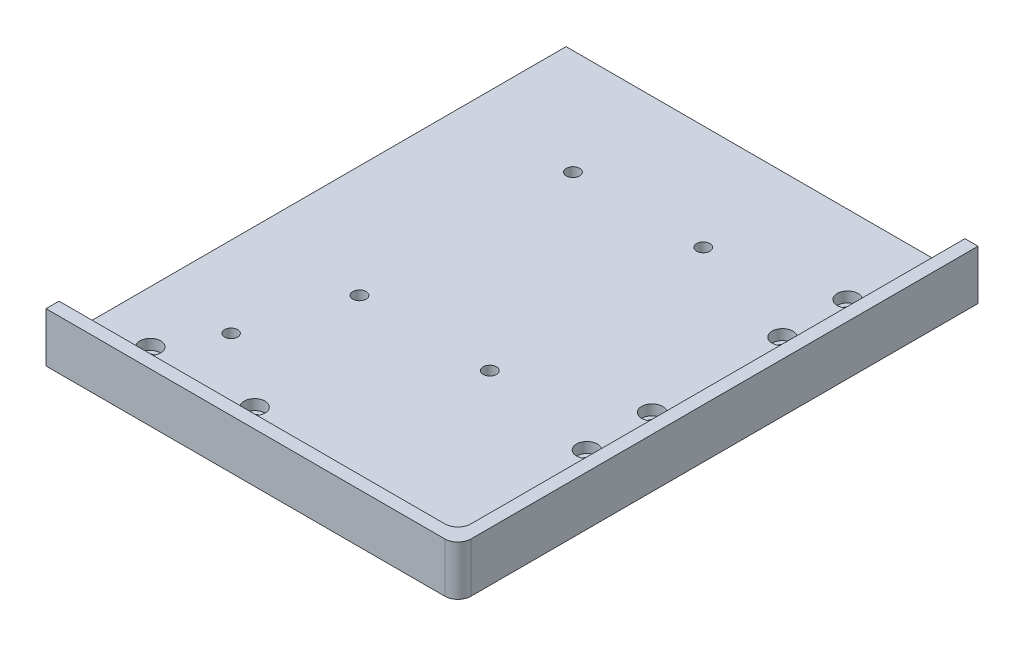
SolidWorks part; units mm, degrees
ref_plane "Front Plane" through (0, 0, 0) normal (0, 0, 1) x (1, 0, 0)
ref_plane "Top Plane" through (0, 0, 0) normal (0, 1, 0) x (1, 0, 0)
ref_plane "Right Plane" through (0, 0, 0) normal (1, 0, 0) x (0, 0, -1)
sketch "Sketch1" plane through (0, 0, 0) normal (0, 1, 0) x (1, 0, 0)
  line L1 (0, 0) -> (158, 0)
  line L2 (0, 0) -> (0, -199.5)
  line L3 (0, -199.5) -> (158, -199.5)
  line L4 (158, 0) -> (158, -199.5)
  dimension "D1" = 158
  dimension "D2" = 199.5
extrude "Boss-Extrude1" add sketch "Sketch1" along normal blind 6.35
sketch "Sketch2" [suppressed] plane through (0, 6.35, 0) normal (0, 1, 0) x (1, 0, 0)
  line L0 (0, -199.5) -> (158, -199.5) construction
  line L1 (158, -199.5) -> (77, -199.5)
  line L2 (158, -199.5) -> (158, -158.5)
  line L3 (158, -158.5) -> (77, -158.5)
  line L4 (77, -199.5) -> (77, -158.5)
  dimension "D1" = 81
  dimension "D2" = 41
sketch "Sketch3" plane through (0, 6.35, 0) normal (0, 1, 0) x (1, 0, 0)
  line L16 (158, -199.5) -> (158, 0) construction
  line L20 (0, -199.5) -> (158, -199.5) construction
  line L21 (158, -199.5) -> (158, 0)
  line L22 (0, -199.5) -> (158, -199.5)
  line L23 (0, -194.5) -> (153, -194.5)
  line L24 (153, -194.5) -> (153, 0)
  line L25 (158, 0) -> (153, 0)
  line L26 (0, -199.5) -> (0, -194.5)
  dimension "D1" = 5
extrude "Boss-Extrude2" add sketch "Sketch3" along normal blind 12.7
sketch "Sketch4" plane through (0, 6.35, 0) normal (0, -1, 0) x (1, 0, 0)
  line L0 (0, 179.5) -> (80, 179.5) construction
  line L1 (0, 0) -> (0, 199.5) construction
  line L3 (0, 199.5) -> (158, 199.5) construction
  line L4 (40, 179.5) -> (40, 188.5903) construction
  line L5 (138, 160) -> (138, 0) construction
  line L7 (158, 0) -> (0, 0) construction
  line L8 (158, 199.5) -> (158, 0) construction
  line L9 (138, 80) -> (152.6176, 80) construction
  point P8 (20, 179.5)
  point P11 (60, 179.5)
  point P20 (138, 130)
  point P21 (138, 105)
  point P22 (138, 30)
  point P23 (138, 80)
  point P24 (138, 55)
  dimension "D1" = 20
  dimension "D2" = 40
  dimension "D3" = 20
  dimension "D4" = 25
  dimension "D5" = 25
  dimension "D6" = 80
  dimension "D7" = 160
hole_wizard "CBORE for M4 SHCS1" positions "Sketch4" profile "Sketch5" counterbore size "M4" standard "ANSI Metric" end condition up to next
sketch "Sketch5" plane through (138, 6.35, 55) normal (1, 0, 0) x (0, 0, 1)
  line L0 (0, 0) -> (0, 6.35)
  line L1 (0, 6.35) -> (2.25, 6.35)
  line L3 (2.25, 6.35) -> (2.25, 4)
  line L4 (2.25, 4) -> (4, 4)
  line L5 (4, 4) -> (4, 0)
  line L7 (4, 0) -> (0, 0)
  line L11 (0, -6.35) -> (0, 107.95) construction
  dimension "Thru Hole Dia." = 4.5
  dimension "Thru Hole Depth" = 6.35
  dimension "C'Bore Dia." = 8
  dimension "C'Bore Depth" = 4
sketch "Sketch7" [suppressed] plane through (0, 0, 0) normal (0, 0, -1) x (-1, 0, 0)
  line L0 (-79, 19.05) -> (-79, 4.7647) construction
  line L1 (-158, 19.05) -> (0, 19.05) construction
  line L2 (-158, 19.05) -> (-158, 0) construction
  line L3 (-129, 19.05) -> (0, 19.05)
  line L4 (-129, 19.05) -> (-129, 9.05)
  line L5 (-129, 9.05) -> (0, 9.05)
  line L6 (0, 19.05) -> (0, 9.05)
  line L7 (0, 19.05) -> (0, 0) construction
  dimension "D2" = 10
  dimension "D3" = 29
extrude "Cut-Extrude2" [suppressed] cut sketch "Sketch7" against normal up to next
fillet "Fillet1" [suppressed] radius 5
sketch "Sketch8" plane through (0, 6.35, 0) normal (0, 1, 0) x (1, 0, 0)
  line L0 (0, -122.25) -> (120.087, -122.25) construction
  line L1 (0, 0) -> (0, -194.5) construction
  line L3 (43, -122.25) -> (43, -40.38) construction
  line L4 (93, -122.25) -> (93, -40.38) construction
  point P6 (43, -122.25)
  point P7 (93, -122.25)
  point P13 (93, -40.38)
  point P14 (43, -40.38)
  dimension "D1" = 77.25
  dimension "D2" = 43
  dimension "D3" = 50
  dimension "D4" = 81.87
hole_wizard "Ø5.1 (5.1) Diameter Hole1" positions "Sketch8" profile "Sketch9" hole size "Ø5.1" standard "ANSI Metric" end condition up to next
sketch "Sketch9" plane through (43, 6.35, 40.38) normal (1, 0, 0) x (0, 0, 1)
  line L0 (0, 0) -> (0, 6.35)
  line L1 (0, 6.35) -> (2.55, 6.35)
  line L2 (2.55, 6.35) -> (2.55, 0)
  line L5 (2.55, 0) -> (0, 0)
  line L11 (0, -6.35) -> (0, 107.95) construction
  dimension "Thru Hole Dia." = 5.1
  dimension "Thru Hole Depth" = 6.35
fillet "Fillet2" radius 5 1 edges at (158, 9.525, 199.5)
fillet "Fillet3" radius 5 1 edges at (153, 12.7, 194.5)
sketch "Sketch10" plane through (0, 6.35, 0) normal (0, 1, 0) x (1, 0, 0)
  line L0 (153, -159.5) -> (74.2575, -159.5) construction
  line L1 (153, 0) -> (153, -189.5) construction
  line L2 (148, -194.5) -> (0, -194.5) construction
  point P4 (143, -159.5)
  point P5 (31, -159.5)
  dimension "D1" = 10
  dimension "D2" = 112
  dimension "D3" = 35
hole_wizard "Ø5.0 (5) Diameter Hole1" positions "Sketch10" profile "Sketch11" hole size "Ø5.0" standard "ANSI Metric" end condition up to next
sketch "Sketch11" plane through (31, 6.35, 159.5) normal (1, 0, 0) x (0, 0, 1)
  line L0 (0, 0) -> (0, 6.35)
  line L1 (0, 6.35) -> (2.5, 6.35)
  line L2 (2.5, 6.35) -> (2.5, 0)
  line L5 (2.5, 0) -> (0, 0)
  line L11 (0, -6.35) -> (0, 107.95) construction
  dimension "Thru Hole Dia." = 5
  dimension "Thru Hole Depth" = 6.35
